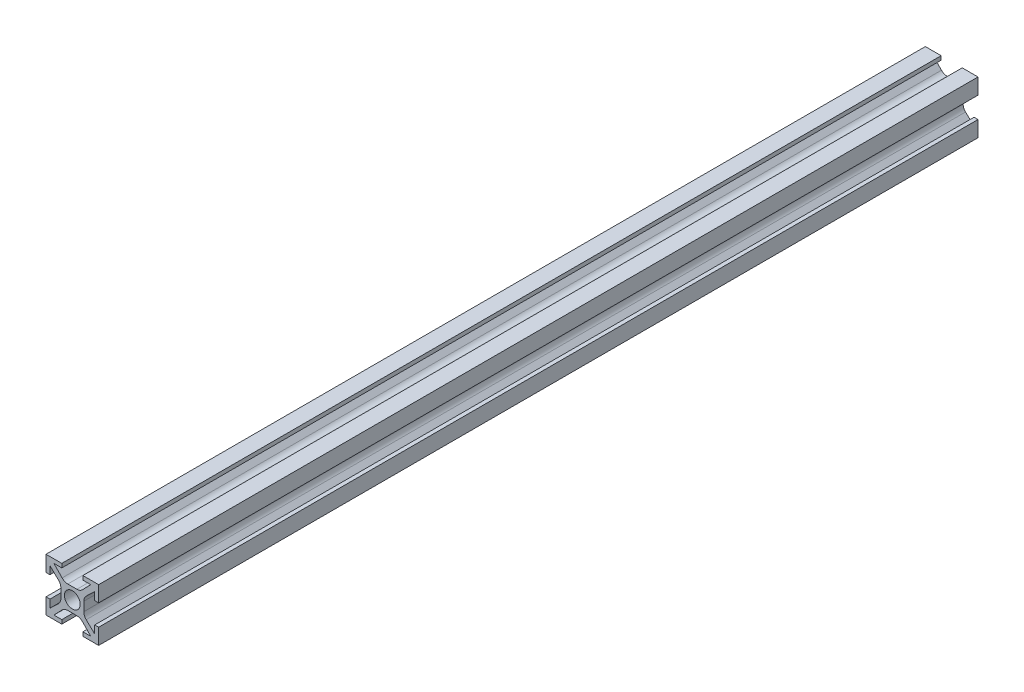
SolidWorks part; units mm, degrees
ref_plane "Plano frontal" through (0, 0, 0) normal (0, 0, 1) x (1, 0, 0)
ref_plane "Plano superior" through (0, 0, 0) normal (0, 1, 0) x (1, 0, 0)
ref_plane "Plano direito" through (0, 0, 0) normal (1, 0, 0) x (0, 0, -1)
sketch "Esboço1" plane through (0, 0, 0) normal (0, 0, 1) x (1, 0, 0)
  line L1 (10, -10) -> (-10, -10)
  line L2 (10, -10) -> (10, 10)
  line L3 (10, 10) -> (-10, 10)
  line L4 (-10, -10) -> (-10, 10)
  line L5 (10, -10) -> (-10, 10) construction
  line L6 (10, 10) -> (-10, -10) construction
  point P0 (0, 0)
  dimension "D1" = 20
  dimension "D2" = 20
extrude "Ressalto-extrusão1" add sketch "Esboço1" along normal blind 334
sketch "Esboço2" plane through (0, 0, 0) normal (0, 0, -1) x (-1, 0, 0)
  line L0 (-12.8371, 0) -> (13.0052, 0) construction
  line L1 (0, -11.8561) -> (0, 11.8) construction
  line L2 (-10, 4) -> (-8.5, 4)
  line L3 (-10, -10) -> (-10, 10) construction
  line L4 (-8.5, 4) -> (-8.5, 7)
  line L5 (-8.5, 7) -> (-4.3538, 3)
  line L6 (-4.3538, 3) -> (-4.3538, -3)
  line L7 (-10, 4) -> (-10, -4)
  line L8 (-8.5, -7) -> (-4.3538, -3)
  line L9 (-8.5, -4) -> (-8.5, -7)
  line L10 (-10, -4) -> (-8.5, -4)
  line L11 (4, 10) -> (4, 8.5)
  line L12 (4, 8.5) -> (7, 8.5)
  line L13 (7, 8.5) -> (3, 4.3538)
  line L14 (3, 4.3538) -> (-3, 4.3538)
  line L15 (4, 10) -> (-4, 10)
  line L16 (-7, 8.5) -> (-3, 4.3538)
  line L17 (-4, 8.5) -> (-7, 8.5)
  line L18 (-4, 10) -> (-4, 8.5)
  line L19 (10, -4) -> (8.5, -4)
  line L20 (8.5, -4) -> (8.5, -7)
  line L21 (8.5, -7) -> (4.3538, -3)
  line L22 (4.3538, -3) -> (4.3538, 3)
  line L23 (10, -4) -> (10, 4)
  line L24 (8.5, 7) -> (4.3538, 3)
  line L25 (8.5, 4) -> (8.5, 7)
  line L26 (10, 4) -> (8.5, 4)
  line L27 (-4, -10) -> (-4, -8.5)
  line L28 (-4, -8.5) -> (-7, -8.5)
  line L29 (-7, -8.5) -> (-3, -4.3538)
  line L30 (-3, -4.3538) -> (3, -4.3538)
  line L31 (-4, -10) -> (4, -10)
  line L32 (7, -8.5) -> (3, -4.3538)
  line L33 (4, -8.5) -> (7, -8.5)
  line L34 (4, -10) -> (4, -8.5)
  circle A0 centre (0, 0) radius 3
  point P17 (-4.3538, 0)
  point P20 (-10, 0)
  point P28 (0, 4.3538)
  point P31 (0, 10)
  point P38 (4.3538, 0)
  point P41 (10, 0)
  point P48 (0, -4.3538)
  point P51 (0, -10)
  dimension "D1" = 6
  dimension "D2" = 4
  dimension "D3" = 3
  dimension "D4" = 1.5
  dimension "D5" = 3
  dimension "D6" = 4
extrude "Corte-extrusão1" cut sketch "Esboço2" against normal through all both and the other way through all
fillet "Filete1" radius 3 8 edges at (-3, -4.3538, 167) (3, -4.3538, 167) (4.3538, -3, 167) (4.3538, 3, 167) (-4.3538, -3, 167) (-4.3538, 3, 167) (-3, 4.3538, 167) (3, 4.3538, 167)
